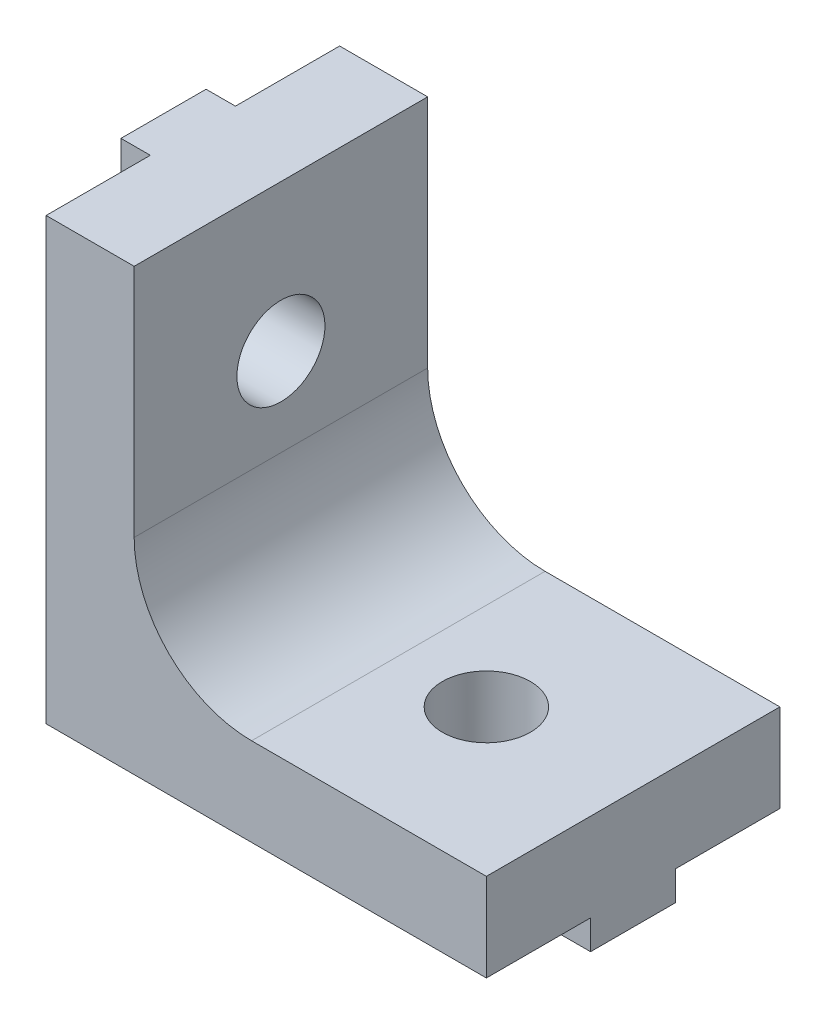
SolidWorks part; units mm, degrees
ref_plane "Front Plane" through (0, 0, 0) normal (0, 0, 1) x (1, 0, 0)
ref_plane "Top Plane" through (0, 0, 0) normal (0, 1, 0) x (1, 0, 0)
ref_plane "Right Plane" through (0, 0, 0) normal (1, 0, 0) x (0, 0, -1)
sketch "Esquisse1" plane through (0, 0, 0) normal (0, 0, 1) x (1, 0, 0)
  line L0 (0, 0) -> (15, 0)
  line L1 (15, 0) -> (15, 3)
  line L2 (15, 3) -> (7, 3)
  line L4 (3, 7) -> (3, 15)
  line L5 (3, 15) -> (0, 15)
  line L6 (0, 15) -> (0, 0)
  arc A0 (7, 3) -> (3, 7) centre (7, 7) cw
  dimension "D1" = 4
  dimension "D2" = 15
  dimension "D3" = 3
extrude "Main" add sketch "Esquisse1" along normal blind 10
sketch "Esquisse4" plane through (0, 0, 0) normal (-1, 0, 0) x (0, 0, 1)
  line L0 (10, 15) -> (0, 15) construction
  line L1 (3.55, 15) -> (6.45, 15)
  line L2 (3.55, 15) -> (3.55, 0)
  line L3 (3.55, 0) -> (6.45, 0)
  line L4 (6.45, 15) -> (6.45, 0)
  line L5 (10, 0) -> (0, 0) construction
  point P8 (5, 15)
  point P9 (5, 15)
  dimension "D1" = 2.9
extrude "MakerBeamFixVertical" add sketch "Esquisse4" along normal blind 1
sketch "Esquisse2" plane through (0, 0, 0) normal (-1, 0, 0) x (0, 0, 1)
  line L0 (10, 15) -> (6.45, 15) construction
  line L1 (10, 15) -> (0, 15) construction
  circle A0 centre (5, 10) radius 1.5
  point P9 (5, 15)
  dimension "D1" = 3
  dimension "D2" = 5
extrude "MakerBeamVerticalHole" cut sketch "Esquisse2" against normal through all both and the other way through all
sketch "Esquisse5" plane through (0, 0, 0) normal (0, -1, 0) x (-1, 0, 0)
  line L0 (-15, -10) -> (-15, 0) construction
  line L1 (0, -3.55) -> (-15, -3.55)
  line L2 (0, -3.55) -> (0, -6.45)
  line L3 (0, -6.45) -> (-15, -6.45)
  line L4 (-15, -3.55) -> (-15, -6.45)
  line L5 (1, -6.45) -> (0, -6.45) construction
extrude "MakerBeamFixHorizontal" add sketch "Esquisse5" along normal blind 1
sketch "Esquisse3" plane through (0, 0, 0) normal (0, -1, 0) x (1, 0, 0)
  line L0 (15, 10) -> (15, 6.45) construction
  line L1 (0, 6.45) -> (0, 3.55) construction
  circle A0 centre (10, 5) radius 1.5
  dimension "D2" = 5
extrude "MakerBeamHorizontalHole" cut sketch "Esquisse3" against normal through all both and the other way through all
